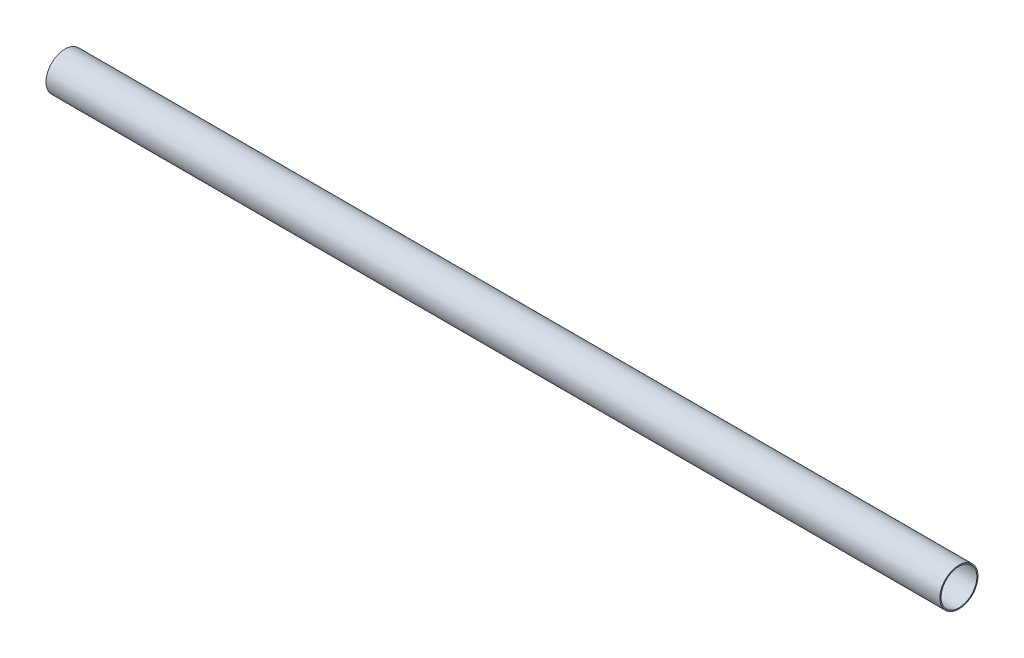
SolidWorks part; units mm, degrees
ref_plane "Front Plane" through (0, 0, 0) normal (0, 0, 1) x (1, 0, 0)
ref_plane "Top Plane" through (0, 0, 0) normal (0, 1, 0) x (1, 0, 0)
ref_plane "Right Plane" through (0, 0, 0) normal (1, 0, 0) x (0, 0, -1)
sketch "Sketch1" plane through (0, 0, 0) normal (1, 0, 0) x (0, 0, -1)
  line L0 (0, 25.4) -> (0, 23.9) construction
  circle A0 centre (0, 0) radius 25.4
  circle A1 centre (0, 0) radius 23.9
  dimension "D1" = 50.8
extrude "Boss-Extrude1" add sketch "Sketch1" along normal blind 1192
